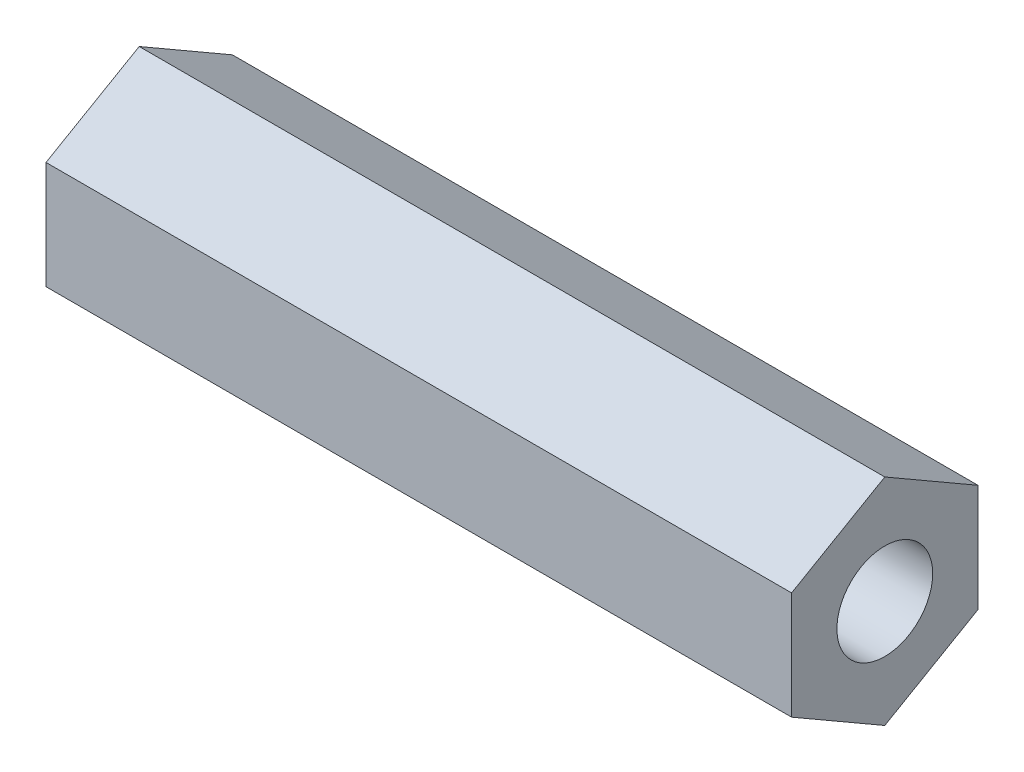
SolidWorks part; units mm, degrees
material "6061 Alloy"
ref_plane "Front Plane" through (0, 0, 0) normal (0, 0, 1) x (1, 0, 0)
ref_plane "Top Plane" through (0, 0, 0) normal (0, 1, 0) x (1, 0, 0)
ref_plane "Right Plane" through (0, 0, 0) normal (1, 0, 0) x (0, 0, -1)
sketch "Sketch1" plane through (0, 0, 0) normal (1, 0, 0) x (0, 0, -1)
  line L1 (0, 7.3323) -> (-6.35, 3.6662)
  line L2 (-6.35, 3.6662) -> (-6.35, -3.6662)
  line L3 (-6.35, -3.6662) -> (0, -7.3323)
  line L4 (0, -7.3323) -> (6.35, -3.6662)
  line L5 (6.35, -3.6662) -> (6.35, 3.6662)
  line L6 (6.35, 3.6662) -> (0, 7.3323)
  circle A0 centre (0, 0) radius 6.35 construction
  circle A1 centre (0, 0) radius 3.2639
  dimension "D1" = 12.7
  dimension "D2" = 6.5278
extrude "Boss-Extrude1" add sketch "Sketch1" along normal blind 50.8
